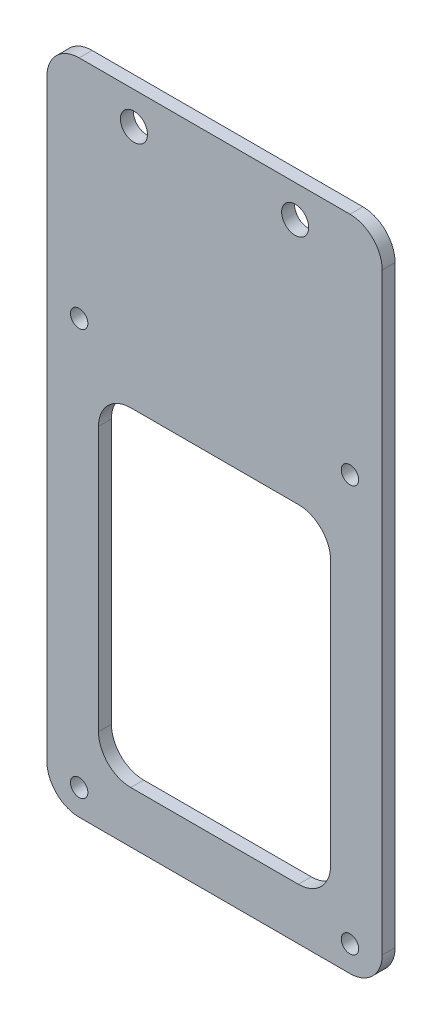
SolidWorks part; units mm, degrees
material "E-玻璃纤维"
ref_plane "前视基准面" through (0, 0, 0) normal (0, 0, 1) x (1, 0, 0)
ref_plane "上视基准面" through (0, 0, 0) normal (0, 1, 0) x (1, 0, 0)
ref_plane "右视基准面" through (0, 0, 0) normal (1, 0, 0) x (0, 0, -1)
sketch "草图1" plane through (0, 0, 0) normal (0, 0, 1) x (1, 0, 0)
  line L1 (-26, -51) -> (26, -51)
  line L2 (-26, -51) -> (-26, 51)
  line L3 (-26, 51) -> (26, 51)
  line L4 (26, -51) -> (26, 51)
  line L5 (-26, -51) -> (26, 51) construction
  line L6 (-26, 51) -> (26, -51) construction
  point P0 (0, 0)
  dimension "D1" = 102
  dimension "D2" = 52
extrude "凸台-拉伸1" add sketch "草图1" along normal blind 2
fillet "圆角1" radius 5 4 edges at (-26, -51, 1) (26, -51, 1) (-26, 51, 1) (26, 51, 1)
sketch "草图2" plane through (0, 0, 2) normal (0, 0, 1) x (1, 0, 0)
  line L0 (0, 81.9714) -> (0, -113.8581) construction
  line L1 (21, 51) -> (-21, 51) construction
  circle A0 centre (-12.5, 46) radius 2.1
  circle A1 centre (12.5, 46) radius 2.1
  circle A2 centre (-21, 16) radius 1.35
  circle A3 centre (21, 16) radius 1.35
  circle A4 centre (-21, -47) radius 1.35
  circle A5 centre (21, -47) radius 1.35
  dimension "D1" = 25
  dimension "D2" = 4.2
  dimension "D4" = 42
  dimension "D5" = 2.7
  dimension "D7" = 63
  dimension "D8" = 2.7
  dimension "D3" = 5
  dimension "D6" = 30
extrude "切除-拉伸1" cut sketch "草图2" against normal through all
sketch "草图3" plane through (0, 0, 2) normal (0, 0, 1) x (1, 0, 0)
  line L0 (0, 58.6091) -> (0, -64.7079) construction
  line L16 (-21, -51) -> (21, -51) construction
  line L22 (-18, 8) -> (18, 8)
  line L23 (-18, 8) -> (-18, -43)
  line L24 (-18, -43) -> (18, -43)
  line L25 (18, 8) -> (18, -43)
  line L26 (-18, 8) -> (18, -43) construction
  line L27 (-18, -43) -> (18, 8) construction
  line L28 (-26, 46) -> (-26, -46) construction
  circle A0 centre (-21, 16) radius 1.35 construction
  point P3 (0, -17.5)
  dimension "D1" = 8
  dimension "D2" = 8
  dimension "D3" = 8
extrude "切除-拉伸2" cut sketch "草图3" against normal blind 10
fillet "圆角2" radius 5 4 edges at (18, -43, 1) (-18, -43, 1) (-18, 8, 1) (18, 8, 1)
